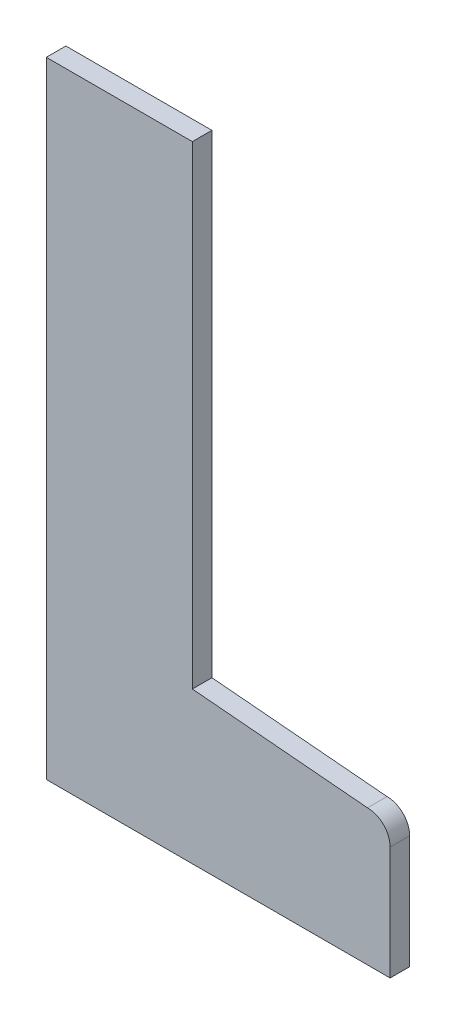
SolidWorks part; units mm, degrees
material "Pine"
ref_plane "Front Plane" through (0, 0, 0) normal (0, 0, 1) x (1, 0, 0)
ref_plane "Top Plane" through (0, 0, 0) normal (0, 1, 0) x (1, 0, 0)
ref_plane "Right Plane" through (0, 0, 0) normal (1, 0, 0) x (0, 0, -1)
sketch "Sketch1" plane through (0, 0, 0) normal (0, 0, 1) x (1, 0, 0)
  line L1 (-101.286, 306.1967) -> (0.1159, 306.1967)
  line L2 (-101.286, 306.1967) -> (-101.286, -74.8033)
  line L3 (-101.286, -74.8033) -> (133.664, -74.8033)
  line L5 (133.664, -74.8033) -> (32.064, -74.8033) construction
  line L6 (141.4222, -74.8033) -> (133.664, -74.8033)
  line L9 (0, 108.2289) -> (20.828, 108.2289) construction
  line L11 (133.664, -74.8033) -> (20.888, -74.8033) construction
  line L20 (20.9439, 111.8867) -> (20.9439, 306.1967)
  line L21 (20.9439, 306.1967) -> (0.1159, 306.1967)
  line L25 (141.4222, -74.8033) -> (141.4222, -5.7254)
  line L28 (20.9439, 111.8867) -> (20.9439, 34.4953)
  line L30 (20.9439, 34.4953) -> (20.9439, 17.413)
  line L31 (141.4222, -5.7254) -> (128.7222, -5.7254) construction
  line L32 (127.6164, 8.0804) -> (20.9439, 17.413)
  circle A0 centre (88.198, -55.7533) radius 3.937 construction
  circle A1 centre (88.198, 1.3967) radius 3.937 construction
  arc A6 (141.4222, -5.7254) -> (127.6164, 8.0804) centre (127.6164, -5.7254) ccw
  dimension "D2" = 7.874
  dimension "D3" = 5
  dimension "D4" = 19.05
  dimension "D6" = 76.2
  dimension "D1" = 12.7
  dimension "D5" = 381
  dimension "D7" = 112.776
extrude "Boss-Extrude1" add sketch "Sketch1" along normal blind 11.9062
sketch "Sketch2" plane through (0, 0, 11.9062) normal (0, 0, 1) x (1, 0, 0)
  line L0 (-101.286, -74.8033) -> (-68.012, -74.8033)
  line L1 (-101.286, -74.8033) -> (141.4222, -74.8033) construction
  line L2 (-68.012, -74.8033) -> (-68.012, 306.1967)
  line L3 (20.9439, 306.1967) -> (-101.286, 306.1967) construction
  line L4 (-68.012, 306.1967) -> (-101.286, 306.1967)
  line L5 (-101.286, 306.1967) -> (-101.286, -74.8033)
  dimension "D1" = 33.274
extrude "Cut-Extrude1" cut sketch "Sketch2" against normal through all
hole_wizard "CSK for #10 Flat Head Machine Screw (100)1" positions "3DSketch1" profile "Sketch3" countersink size "#10" standard "ANSI Inch"
sketch3d "3DSketch1"
  dimension "D5" = 21.59
  dimension "D1" = 127
  dimension "D2" = 127
  dimension "D3" = 342.9
  dimension "D4" = 215.9
  dimension "D6" = 76.2
  dimension "D7" = 111.506
  dimension "D8" = 166.116
sketch "Sketch3" plane through (119.8322, -0.0386, 0) normal (1, 0, 0) x (0, 1, 0)
  line L0 (0, 0) -> (0, 52.3338)
  line L1 (0, 52.3338) -> (2.5527, 50.8)
  line L2 (2.5527, 50.8) -> (2.5527, 1.9608)
  line L3 (2.5527, 1.9608) -> (4.8895, 0)
  line L5 (4.8895, 0) -> (0, 0)
  line L6 (-2.5527, 1.9608) -> (-4.8895, 0) construction
  line L10 (0, 52.3338) -> (-2.5527, 50.8) construction
  line L11 (0, -6.35) -> (0, 107.95) construction
  dimension "Hole Dia." = 5.1054
  dimension "Hole Depth" = 50.8
  dimension "Near C'Sink Dia." = 9.779
  dimension "Near C'Sink Angle" = 100
  dimension "Drill Angle" = 118
equation "\"D5@3DSketch1\"=17-16.15"
equation "\"D7@3DSketch1\"=17-12.61"
